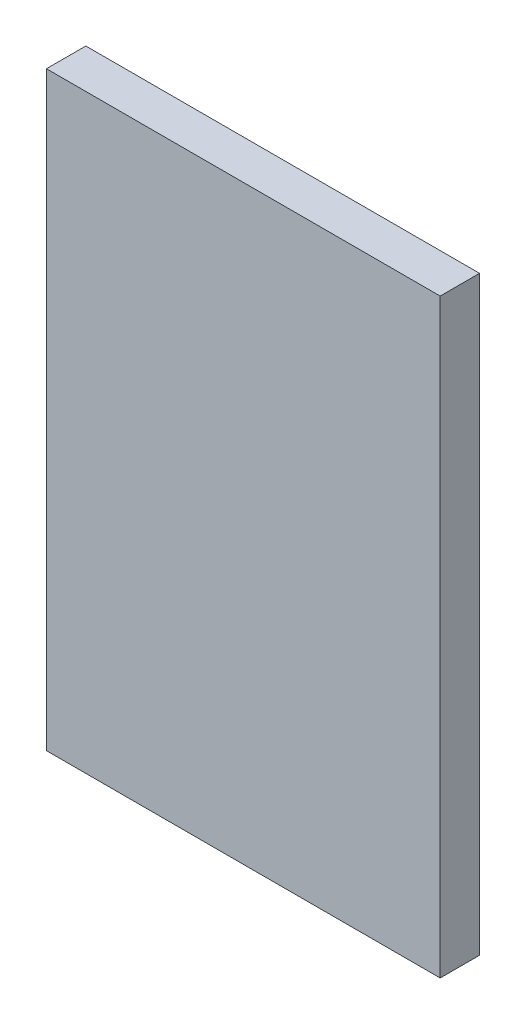
SolidWorks part; units mm, degrees
ref_plane "Front Plane" through (0, 0, 0) normal (0, 0, 1) x (1, 0, 0)
ref_plane "Top Plane" through (0, 0, 0) normal (0, 1, 0) x (1, 0, 0)
ref_plane "Right Plane" through (0, 0, 0) normal (1, 0, 0) x (0, 0, -1)
sketch "Sketch1" plane through (0, 0, 0) normal (0, 0, 1) x (1, 0, 0)
  line L1 (0, 0) -> (20, 0)
  line L2 (0, 0) -> (0, 30)
  line L3 (0, 30) -> (20, 30)
  line L4 (20, 0) -> (20, 30)
  line L5 (10, 30) -> (10, 0) construction
  line L6 (0, 15) -> (20, 15) construction
  point P68 (10, 15)
  dimension "D1" = 20
  dimension "D2" = 30
extrude "Boss-Extrude1" add sketch "Sketch1" along normal blind 2
